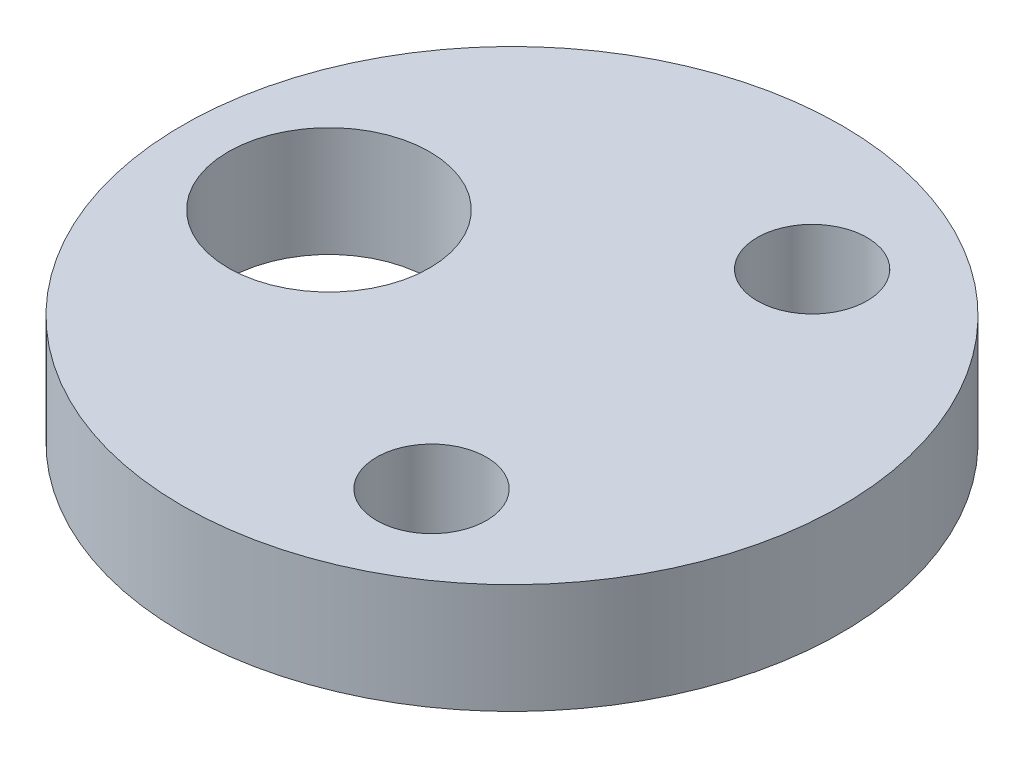
SolidWorks part; units mm, degrees
ref_plane "Front Plane" through (0, 0, 0) normal (0, 0, 1) x (1, 0, 0)
ref_plane "Top Plane" through (0, 0, 0) normal (0, 1, 0) x (1, 0, 0)
ref_plane "Right Plane" through (0, 0, 0) normal (1, 0, 0) x (0, 0, -1)
sketch "Sketch1" plane through (0, 0, 0) normal (0, 1, 0) x (1, 0, 0)
  circle A0 centre (0, 0) radius 9
  circle A1 centre (2.9991, -5.1967) radius 1.5
  circle A2 centre (3.0009, 5.1957) radius 1.5
  circle A3 centre (-5, 0.0008) radius 2.75
  dimension "D1" = 18
  dimension "D3" = 5.5
  dimension "D5" = 3
  dimension "D7" = 3
  dimension "D2" = 5
  dimension "D4" = 6
  dimension "D6" = 6
extrude "Boss-Extrude1" add sketch "Sketch1" along normal blind 3
